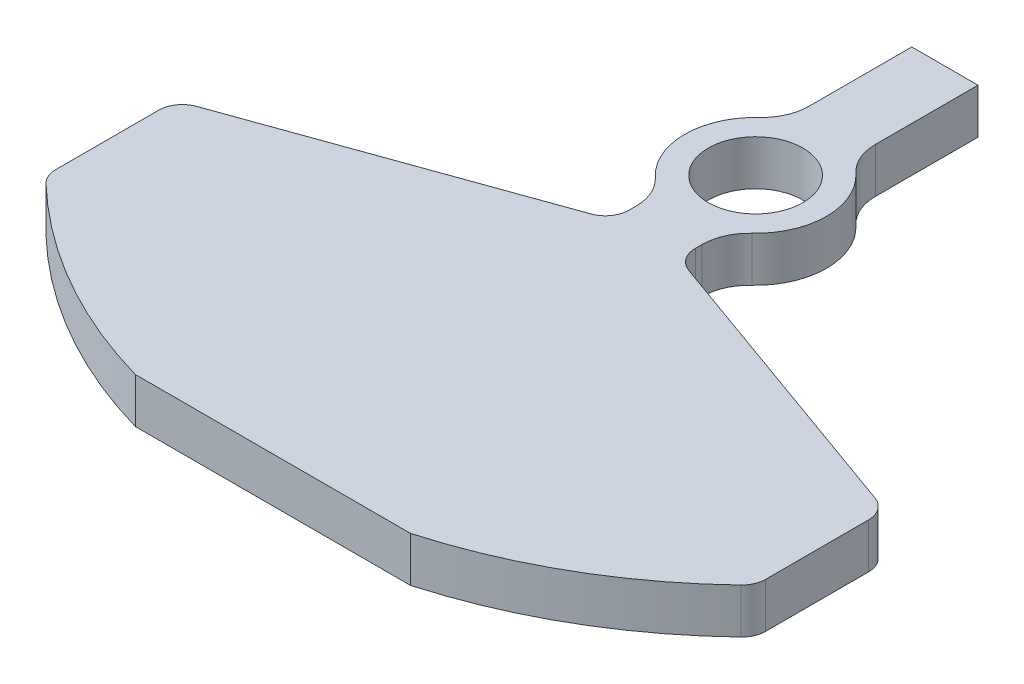
SolidWorks part; units mm, degrees
material "AISI 1020 Steel, Cold Rolled"
ref_plane "Front Plane" through (0, 0, 0) normal (0, 0, 1) x (1, 0, 0)
ref_plane "Top Plane" through (0, 0, 0) normal (0, 1, 0) x (1, 0, 0)
ref_plane "Right Plane" through (0, 0, 0) normal (1, 0, 0) x (0, 0, -1)
sketch "Sketch1" plane through (0, 0, 0) normal (0, 1, 0) x (1, 0, 0)
  line L0 (0, 0) -> (0, 70.2594) construction
  line L1 (-7, 40) -> (7, 40)
  line L2 (-7, 40) -> (-7, 13.2665)
  line L3 (7, 40) -> (7, 13.2665)
  line L4 (-7, -13.2665) -> (-7, -23.2665)
  line L5 (-29.0861, -102) -> (29.0861, -102)
  line L7 (-75, -47.6323) -> (-75, -75)
  line L8 (-75, -47.6323) -> (-7, -23.2665)
  line L9 (75, -47.6323) -> (75, -75)
  line L12 (7, -13.2665) -> (7, -23.2665)
  line L13 (7, -23.2665) -> (75, -47.6323)
  circle A0 centre (0, 0) radius 10
  arc A1 (-7, 13.2665) -> (-7, -13.2665) centre (0, 0) ccw
  arc A2 (7, -13.2665) -> (7, 13.2665) centre (0, 0) ccw
  arc A3 (-75, -75) -> (-29.0861, -102) centre (0, 0) ccw
  arc A4 (29.0861, -102) -> (75, -75) centre (0, 0) ccw
  point P15 (0, -100)
  dimension "D1" = 20
  dimension "D4" = 30
  dimension "D9" = 102
  dimension "D2" = 14
  dimension "D3" = 7
  dimension "D5" = 40
  dimension "D6" = 75
  dimension "D7" = 150
  dimension "D8" = 10
extrude "Boss-Extrude1" add sketch "Sketch1" along normal blind 9.525
fillet "Fillet1" radius 10 4 edges at (-7, 4.7625, -13.2665) (7, 4.7625, -13.2665) (7, 4.7625, 13.2665) (-7, 4.7625, 13.2665)
fillet "Fillet2" radius 5 6 edges at (-75, 4.7625, 75) (75, 4.7625, 47.6323) (-75, 4.7625, 47.6323) (-7, 4.7625, 23.2665) (75, 4.7625, 75) (7, 4.7625, 23.2665)
hole_wizard "M8x1.25 Tapped Hole1" positions "Sketch3" profile "Sketch2" tap size "M8x1.25" standard "ANSI Metric"
sketch "Sketch3" plane through (0, 0, -40) normal (0, 0, -1) x (-1, 0, 0)
  line L0 (-7, 4.7625) -> (7, 4.7625) construction
  line L1 (-7, 9.525) -> (-7, 0) construction
  line L2 (7, 9.525) -> (7, 0) construction
  point P0 (0, 4.7625)
  dimension "D1" = 0
sketch "Sketch2" plane through (0, 4.7625, -40) normal (1, 0, 0) x (0, 1, 0)
  line L0 (0, 0) -> (0, 24.2929)
  line L1 (0, 24.2929) -> (3.4, 22.25)
  line L2 (3.4, 22.25) -> (3.4, 0)
  line L5 (3.4, 0) -> (0, 0)
  line L10 (0, 24.2929) -> (-3.4, 22.25) construction
  line L11 (0, -6.35) -> (0, 107.95) construction
  dimension "Tap Drill Dia." = 6.8
  dimension "Tap Drill Depth" = 22.25
  dimension "Drill Angle" = 118
